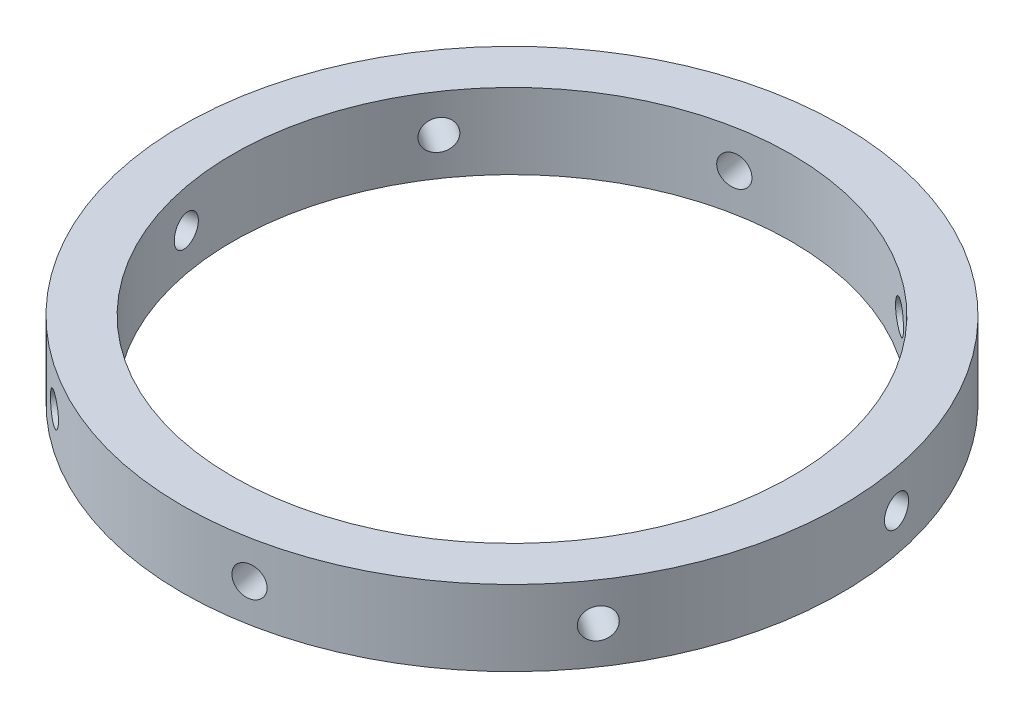
SolidWorks part; units mm, degrees
ref_plane "Front Plane" through (0, 0, 0) normal (0, 0, 1) x (1, 0, 0)
ref_plane "Top Plane" through (0, 0, 0) normal (0, 1, 0) x (1, 0, 0)
ref_plane "Right Plane" through (0, 0, 0) normal (1, 0, 0) x (0, 0, -1)
sketch "Sketch1" plane through (0, 0, 0) normal (0, 1, 0) x (1, 0, 0)
  circle A0 centre (0, 0) radius 55.5
  circle A1 centre (0, 0) radius 65.5
  dimension "D1" = 111
  dimension "D2" = 10
extrude "Boss-Extrude1" add sketch "Sketch1" against normal blind 15
hole_wizard "Ø6.0 (6) Diameter Hole2" positions "3DSketch1" profile "Sketch3" hole size "Ø6.0" standard "ANSI Metric"
sketch3d "3DSketch1"
  circle A0 centre (0, 0, 0) radius 65.5 construction
  circle A2 centre (0, 0, 0) radius 65.5
  point P0 (12.142, -7.5, 64.3648)
  point P5 (0, 65.5, 0)
  point P10 (0, 65.5, 0)
  dimension "D1" = 7.5
sketch "Sketch3" plane through (12.142, -7.5, 64.3648) normal (0, 1, 0) x (0.9827, 0, -0.1854)
  line L0 (0, 0) -> (0, 67.3016)
  line L1 (0, 67.3016) -> (3, 65.499)
  line L2 (3, 65.499) -> (3, 0)
  line L5 (3, 0) -> (0, 0)
  line L10 (0, 67.3016) -> (-3, 65.499) construction
  line L11 (0, -6.35) -> (0, 107.95) construction
  dimension "Hole Dia." = 6
  dimension "Hole Depth" = 65.499
  dimension "Drill Angle" = 118
pattern_circular "CirPattern1" count 8 over 360 about axis through (0, 0, 0) along (0, 1, 0) of "Ø6.0 (6) Diameter Hole2"
